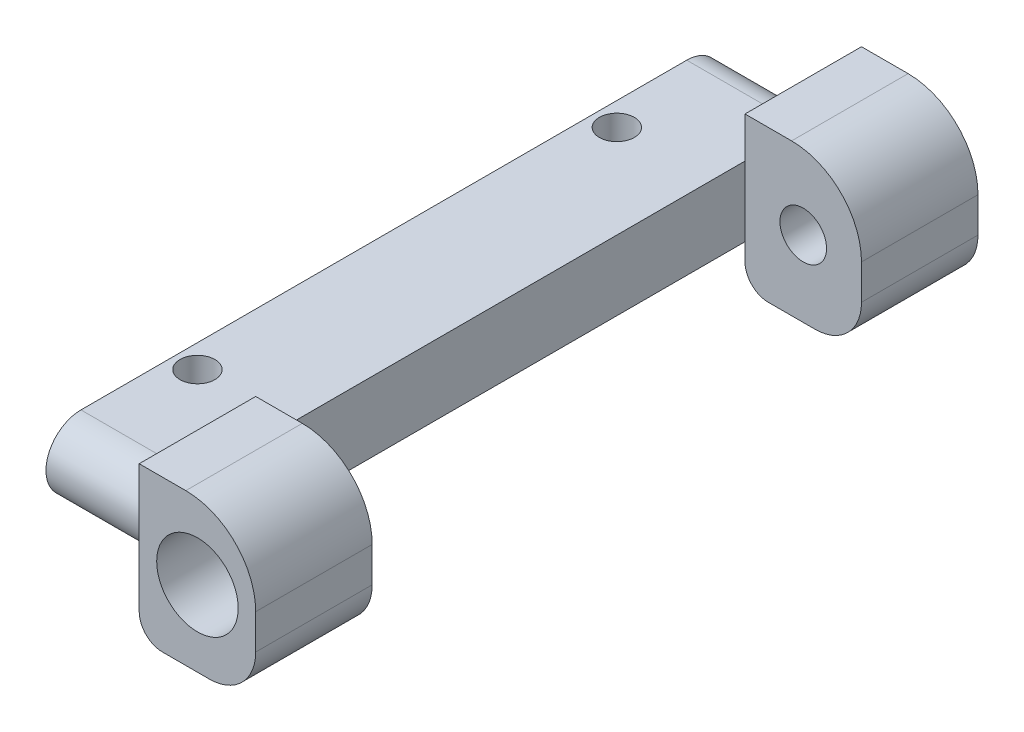
SolidWorks part; units mm, degrees
ref_plane "Alzado" through (0, 0, 0) normal (0, 0, 1) x (1, 0, 0)
ref_plane "Planta" through (0, 0, 0) normal (0, 1, 0) x (1, 0, 0)
ref_plane "Vista lateral" through (0, 0, 0) normal (1, 0, 0) x (0, 0, -1)
sketch "Croquis1" plane through (0, 0, 0) normal (1, 0, 0) x (0, 0, -1)
  line L0 (-13, 0) -> (13, 0) construction
  line L1 (-13, 1.5) -> (13, 1.5)
  line L2 (-13, -1.5) -> (13, -1.5)
  arc A0 (-13, 1.5) -> (-13, -1.5) centre (-13, 0) ccw
  arc A1 (13, -1.5) -> (13, 1.5) centre (13, 0) ccw
  point P2 (0, 0)
  dimension "D1" = 26
  dimension "D2" = 3
extrude "Saliente-Extruir1" add sketch "Croquis1" along normal blind 5
ref_plane "Plano1" through (5, 0, 0) normal (1, 0, 0) x (0, 0, -1)
sketch "Croquis2" plane through (5, 0, 0) normal (1, 0, 0) x (0, 0, -1)
  line L0 (0, 0) -> (0, 0.8312) construction
  line L1 (-15.5, 3.25) -> (-10.5, 3.25)
  line L2 (-15.5, 3.25) -> (-15.5, -3.25)
  line L3 (-15.5, -3.25) -> (-10.5, -3.25)
  line L4 (-10.5, 3.25) -> (-10.5, -3.25)
  line L5 (-15.5, 3.25) -> (-10.5, -3.25) construction
  line L6 (-15.5, -3.25) -> (-10.5, 3.25) construction
  line L7 (15.5, -3.25) -> (10.5, -3.25)
  line L8 (15.5, 3.25) -> (15.5, -3.25)
  line L9 (15.5, 3.25) -> (10.5, 3.25)
  line L10 (10.5, 3.25) -> (10.5, -3.25)
  point P0 (-13, 0)
  dimension "D1" = 5
  dimension "D2" = 6.5
extrude "Saliente-Extruir3" add sketch "Croquis2" along normal blind 5
fillet "Redondeo1" radius 3 2 edges at (10, 3.25, 13) (10, 3.25, -13)
fillet "Redondeo2" radius 2 2 edges at (10, -3.25, -13) (10, -3.25, 13)
fillet "Redondeo3" radius 1 2 edges at (5, -3.25, 13) (5, -3.25, -13)
ref_plane "Plano2" through (0, 0, -15.5) normal (0, 0, -1) x (-1, 0, 0)
sketch "Croquis4" plane through (0, 0, -15.5) normal (0, 0, -1) x (-1, 0, 0)
  circle A0 centre (-7.5, 0) radius 1.75
  dimension "D1" = 3.5
extrude "Cortar-Extruir1" cut sketch "Croquis4" against normal blind 2.5
ref_plane "Plano4" through (0, 0, 0) normal (0, 0, 1) x (1, 0, 0)
ref_plane "Plano5" through (0, 0, -13) normal (0, 0, -1) x (-1, 0, 0)
sketch "Croquis5" plane through (0, 0, -13) normal (0, 0, -1) x (-1, 0, 0)
  circle A0 centre (-7.5, 0) radius 1
  dimension "D1" = 2
extrude "Cortar-Extruir2" cut sketch "Croquis5" against normal blind 2.5
mirror "Simetría2" about plane through (0, 0, 0) normal (0, 0, 1) of "Cortar-Extruir1", "Cortar-Extruir2"
ref_plane "Plano6" through (0, 1.5, 0) normal (0, 1, 0) x (1, 0, 0)
sketch "Croquis6" plane through (0, 1.5, 0) normal (0, 1, 0) x (1, 0, 0)
  line L0 (5, 10.5) -> (5, -10.5) construction
  line L3 (1, 21.455) -> (1, -2.6113) construction
  line L4 (5, 13) -> (0, 13) construction
  line L6 (0, 0) -> (3.4753, 0) construction
  line L7 (0, 13) -> (0, -13) construction
  circle A0 centre (1, 9) radius 0.75
  circle A1 centre (1, -9) radius 0.75
  point P6 (1, 9)
  dimension "D3" = 1.5
  dimension "D1" = 4
  dimension "D2" = 4
extrude "Cortar-Extruir3" cut sketch "Croquis6" against normal blind 5
